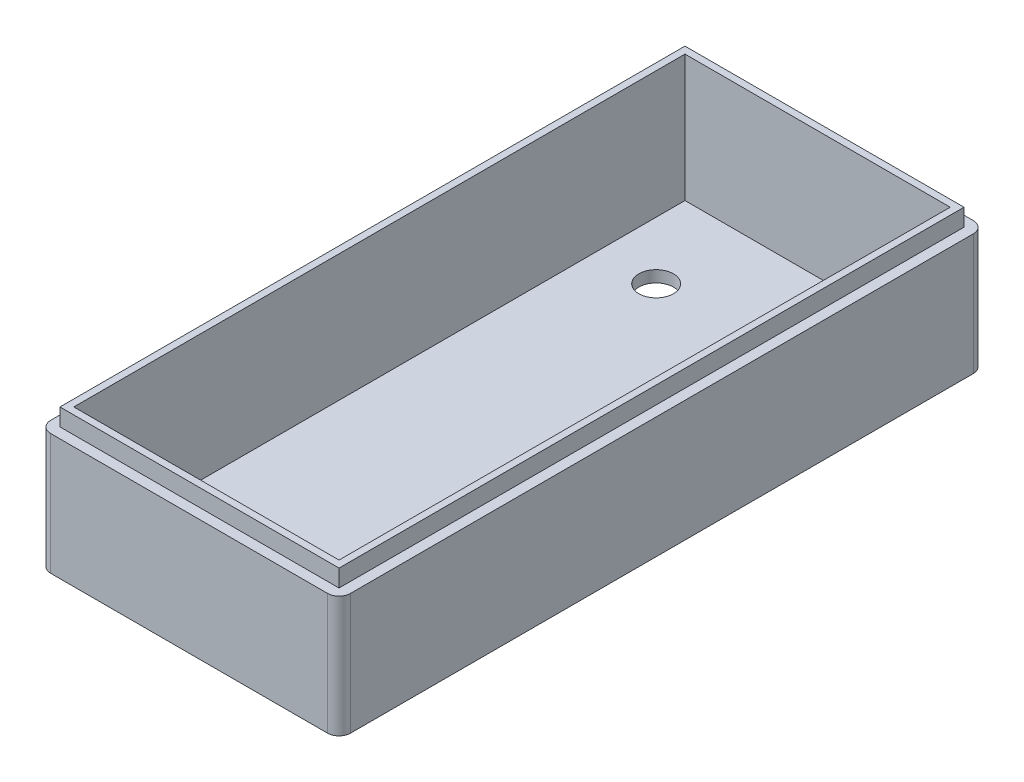
SolidWorks part; units mm, degrees
ref_plane "Front Plane" through (0, 0, 0) normal (0, 0, 1) x (1, 0, 0)
ref_plane "Top Plane" through (0, 0, 0) normal (0, 1, 0) x (1, 0, 0)
ref_plane "Right Plane" through (0, 0, 0) normal (1, 0, 0) x (0, 0, -1)
sketch "Sketch1" plane through (0, 0, 0) normal (0, 1, 0) x (1, 0, 0)
  line L1 (-77.0226, 53.0801) -> (-27.0226, 53.0801)
  line L2 (-77.0226, 53.0801) -> (-77.0226, -56.9199)
  line L3 (-77.0226, -56.9199) -> (-27.0226, -56.9199)
  line L4 (-27.0226, 53.0801) -> (-27.0226, -56.9199)
  dimension "D1" = 110
  dimension "D2" = 50
extrude "Boss-Extrude1" add sketch "Sketch1" along normal blind 2
sketch "Sketch2" plane through (0, 2, 0) normal (0, 1, 0) x (1, 0, 0)
  line L0 (-75.0226, 51.0801) -> (-75.0226, -54.9199)
  line L1 (-77.0226, 53.0801) -> (-27.0226, 53.0801)
  line L2 (-77.0226, 53.0801) -> (-77.0226, -56.9199)
  line L3 (-77.0226, -56.9199) -> (-27.0226, -56.9199)
  line L4 (-27.0226, 53.0801) -> (-27.0226, -56.9199)
  line L5 (-75.0226, -54.9199) -> (-29.0226, -54.9199)
  line L6 (-29.0226, 51.0801) -> (-29.0226, -54.9199)
  line L7 (-75.0226, 51.0801) -> (-29.0226, 51.0801)
  dimension "D1" = 2
extrude "Boss-Extrude3" add sketch "Sketch2" along normal blind 11
sketch "Sketch3" plane through (0, 2, 0) normal (0, 1, 0) x (1, 0, 0)
  circle A0 centre (-31.0226, 42.3801) radius 1.2
  circle A1 centre (-31.0226, -52.9199) radius 1.2
  circle A2 centre (-56.3226, 42.3801) radius 1.2
  circle A3 centre (-56.3226, -52.9199) radius 1.2
extrude "Boss-Extrude4" add sketch "Sketch3" along normal blind 11
sketch "Sketch4" plane through (0, 13, 0) normal (0, 1, 0) x (1, 0, 0)
  line L8 (-26.0226, 54.0801) -> (-78.0226, 54.0801)
  line L9 (-78.0226, 54.0801) -> (-78.0226, -57.9199)
  line L10 (-78.0226, -57.9199) -> (-26.0226, -57.9199)
  line L11 (-26.0226, -57.9199) -> (-26.0226, 54.0801)
  line L12 (-26.0226, 54.0801) -> (-78.0226, 54.0801)
  line L13 (-78.0226, 54.0801) -> (-78.0226, -57.9199)
  line L14 (-78.0226, -57.9199) -> (-26.0226, -57.9199)
  line L15 (-26.0226, -57.9199) -> (-26.0226, 54.0801)
  dimension "D1" = 3
extrude "Extrude-Thin1" add sketch "Sketch4" against normal blind 13 thin thin type one direction reverse wall 1
fillet "Fillet2" radius 2 4 edges at (-78.0226, 6.5, -54.0801) (-26.0226, 6.5, -54.0801) (-26.0226, 6.5, 57.9199) (-78.0226, 6.5, 57.9199)
sketch "Sketch5" plane through (0, 13, 0) normal (0, 1, 0) x (1, 0, 0)
  line L8 (-28.0226, 52.8801) -> (-76.0226, 52.8801)
  line L9 (-76.8226, 52.0801) -> (-76.8226, -55.9199)
  line L10 (-76.0226, -56.7199) -> (-28.0226, -56.7199)
  line L11 (-27.2226, -55.9199) -> (-27.2226, 52.0801)
  line L12 (-28.0226, 52.8801) -> (-76.0226, 52.8801)
  line L13 (-76.8226, 52.0801) -> (-76.8226, -55.9199)
  line L14 (-76.0226, -56.7199) -> (-28.0226, -56.7199)
  line L15 (-27.2226, -55.9199) -> (-27.2226, 52.0801)
  arc A8 (-76.0226, 52.8801) -> (-76.8226, 52.0801) centre (-76.0226, 52.0801) ccw
  arc A9 (-76.8226, -55.9199) -> (-76.0226, -56.7199) centre (-76.0226, -55.9199) ccw
  arc A10 (-28.0226, -56.7199) -> (-27.2226, -55.9199) centre (-28.0226, -55.9199) ccw
  arc A11 (-27.2226, 52.0801) -> (-28.0226, 52.8801) centre (-28.0226, 52.0801) ccw
  arc A12 (-76.0226, 52.8801) -> (-76.8226, 52.0801) centre (-76.0226, 52.0801) ccw
  arc A13 (-76.8226, -55.9199) -> (-76.0226, -56.7199) centre (-76.0226, -55.9199) ccw
  arc A14 (-28.0226, -56.7199) -> (-27.2226, -55.9199) centre (-28.0226, -55.9199) ccw
  arc A15 (-27.2226, 52.0801) -> (-28.0226, 52.8801) centre (-28.0226, 52.0801) ccw
  dimension "D1" = 1.2
extrude "Extrude-Thin3" add sketch "Sketch5" along normal blind 3 thin
sketch "Sketch6" plane through (0, 2, 0) normal (0, 1, 0) x (1, 0, 0)
  circle A0 centre (-56.3226, -52.9199) radius 1.8
  circle A1 centre (-31.0226, -52.9199) radius 1.8
  circle A2 centre (-56.3226, 42.3801) radius 1.8
  circle A3 centre (-31.0226, 42.3801) radius 1.8
extrude "Boss-Extrude5" add sketch "Sketch6" along normal blind 2.8
sketch "Sketch7" plane through (0, 2, 0) normal (0, 1, 0) x (1, 0, 0)
  line L0 (-31.0226, -52.9199) -> (-31.0226, -48.6199)
  line L1 (-31.0226, -48.6199) -> (-18.3371, -48.6199)
sketch "Sketch8" plane through (-26.0226, 0, 0) normal (1, 0, 0) x (0, 0, -1)
  line L0 (-52.9199, 2) -> (-48.6199, 2) construction
  line L2 (-48.6199, 2) -> (-40.6199, 2)
  line L3 (-48.6199, 2) -> (-48.6199, 5.6)
  line L4 (-48.6199, 5.6) -> (-40.6199, 5.6)
  line L5 (-40.6199, 2) -> (-40.6199, 5.6)
  dimension "D1" = 8
  dimension "D2" = 3.6
extrude "Cut-Extrude2" cut sketch "Sketch8" against normal blind 12.8
sketch "Sketch11" plane through (-78.0226, 0, 0) normal (-1, 0, 0) x (0, 0, 1)
  line L0 (-51.0801, 2) -> (54.9199, 2) construction
  line L1 (-50.0801, 7.8) -> (-36.9801, 7.8)
  line L2 (-50.0801, 7.8) -> (-50.0801, 2)
  line L3 (-50.0801, 2) -> (-36.9801, 2)
  line L4 (-36.9801, 7.8) -> (-36.9801, 2)
  line L5 (-51.0801, 13) -> (-51.0801, 2) construction
  dimension "D1" = 5.8
  dimension "D2" = 13.1
  dimension "D3" = 0
  dimension "D4" = 1
extrude "Cut-Extrude5" cut sketch "Sketch11" against normal blind 3
sketch "Sketch12" plane through (0, 0, 57.9199) normal (0, 0, 1) x (1, 0, 0)
  line L0 (-78.0226, 0) -> (-78.0226, 16) construction
  line L1 (-88.0226, 10.3909) -> (-18.0226, 10.3909)
  line L2 (-88.0226, 10.3909) -> (-88.0226, 20.3641)
  line L3 (-88.0226, 20.3641) -> (-18.0226, 20.3641)
  line L4 (-18.0226, 10.3909) -> (-18.0226, 20.3641)
  dimension "D1" = 70
  dimension "D2" = 10
extrude "Cut-Extrude6" cut sketch "Sketch12" against normal blind 130
sketch "Sketch13" plane through (0, 2, 0) normal (0, 1, 0) x (1, 0, 0)
  line L1 (-75.0226, 51.0801) -> (-29.0226, 51.0801)
  line L2 (-75.0226, 51.0801) -> (-75.0226, -54.9199)
  line L3 (-75.0226, -54.9199) -> (-29.0226, -54.9199)
  line L4 (-29.0226, 51.0801) -> (-29.0226, -54.9199)
extrude "Cut-Extrude7" cut sketch "Sketch13" along normal blind 130
sketch "Sketch15" plane through (0, 10.3909, 0) normal (0, 1, 0) x (1, 0, 0)
  line L8 (-76.0226, -57.9199) -> (-28.0226, -57.9199)
  line L9 (-26.0226, -55.9199) -> (-26.0226, 52.0801)
  line L10 (-28.0226, 54.0801) -> (-76.0226, 54.0801)
  line L11 (-78.0226, 52.0801) -> (-78.0226, -55.9199)
  line L12 (-76.0226, -57.9199) -> (-28.0226, -57.9199)
  line L13 (-26.0226, -55.9199) -> (-26.0226, 52.0801)
  line L14 (-28.0226, 54.0801) -> (-76.0226, 54.0801)
  line L15 (-78.0226, 52.0801) -> (-78.0226, -55.9199)
  line L20 (-75.0226, -54.9199) -> (-29.0226, -54.9199)
  line L21 (-29.0226, -54.9199) -> (-29.0226, 51.0801)
  line L22 (-29.0226, 51.0801) -> (-75.0226, 51.0801)
  line L23 (-75.0226, 51.0801) -> (-75.0226, -54.9199)
  line L24 (-75.0226, -54.9199) -> (-29.0226, -54.9199)
  line L25 (-29.0226, -54.9199) -> (-29.0226, 51.0801)
  line L26 (-29.0226, 51.0801) -> (-75.0226, 51.0801)
  line L27 (-75.0226, 51.0801) -> (-75.0226, -54.9199)
  arc A8 (-78.0226, -55.9199) -> (-76.0226, -57.9199) centre (-76.0226, -55.9199) ccw
  arc A9 (-28.0226, -57.9199) -> (-26.0226, -55.9199) centre (-28.0226, -55.9199) ccw
  arc A10 (-26.0226, 52.0801) -> (-28.0226, 54.0801) centre (-28.0226, 52.0801) ccw
  arc A11 (-76.0226, 54.0801) -> (-78.0226, 52.0801) centre (-76.0226, 52.0801) ccw
  arc A12 (-78.0226, -55.9199) -> (-76.0226, -57.9199) centre (-76.0226, -55.9199) ccw
  arc A13 (-28.0226, -57.9199) -> (-26.0226, -55.9199) centre (-28.0226, -55.9199) ccw
  arc A14 (-26.0226, 52.0801) -> (-28.0226, 54.0801) centre (-28.0226, 52.0801) ccw
  arc A15 (-76.0226, 54.0801) -> (-78.0226, 52.0801) centre (-76.0226, 52.0801) ccw
  dimension "D1" = 0
  dimension "D2" = 0
extrude "Boss-Extrude6" add sketch "Sketch15" along normal blind 60
sketch "Sketch16" plane through (0, 0, 57.9199) normal (0, 0, 1) x (1, 0, 0)
  line L0 (-76.0226, 0) -> (-28.0226, 0) construction
  line L1 (-84.3923, 79.1661) -> (-12.6524, 79.1661)
  line L2 (-84.3923, 79.1661) -> (-84.3923, 24)
  line L3 (-84.3923, 24) -> (-12.6524, 24)
  line L4 (-12.6524, 79.1661) -> (-12.6524, 24)
  dimension "D1" = 24
extrude "Cut-Extrude8" cut sketch "Sketch16" against normal blind 130
sketch "Sketch17" plane through (0, 24, 0) normal (0, 1, 0) x (1, 0, 0)
  line L16 (-76.2226, -56.1199) -> (-27.8226, -56.1199)
  line L17 (-27.8226, -56.1199) -> (-27.8226, 52.2801)
  line L18 (-27.8226, 52.2801) -> (-76.2226, 52.2801)
  line L19 (-76.2226, 52.2801) -> (-76.2226, -56.1199)
  line L20 (-76.2226, -56.1199) -> (-27.8226, -56.1199)
  line L21 (-27.8226, -56.1199) -> (-27.8226, 52.2801)
  line L22 (-27.8226, 52.2801) -> (-76.2226, 52.2801)
  line L23 (-76.2226, 52.2801) -> (-76.2226, -56.1199)
  dimension "D1" = 1.2
extrude "Cut-Extrude-Thin1" cut sketch "Sketch17" against normal blind 3 thin
sketch "Sketch18" plane through (0, 7.8, 0) normal (0, -1, 0) x (1, 0, 0)
  line L1 (-75.0226, -36.9801) -> (-78.0226, -36.9801)
  line L2 (-75.0226, -36.9801) -> (-75.0226, -50.0801)
  line L3 (-75.0226, -50.0801) -> (-78.0226, -50.0801)
  line L4 (-78.0226, -36.9801) -> (-78.0226, -50.0801)
extrude "Boss-Extrude7" add sketch "Sketch18" along normal blind 7
sketch "Sketch19" plane through (0, 5.6, 0) normal (0, -1, 0) x (1, 0, 0)
  line L1 (-29.0226, 48.6199) -> (-26.0226, 48.6199)
  line L2 (-29.0226, 48.6199) -> (-29.0226, 40.6199)
  line L3 (-29.0226, 40.6199) -> (-26.0226, 40.6199)
  line L4 (-26.0226, 48.6199) -> (-26.0226, 40.6199)
extrude "Boss-Extrude8" add sketch "Sketch19" along normal blind 4.5
sketch "Sketch20" plane through (0, 2, 0) normal (0, 1, 0) x (1, 0, 0)
  line L4 (-29.0226, 51.0801) -> (-75.0226, 51.0801) construction
  line L5 (-75.0226, -54.9199) -> (-29.0226, -54.9199) construction
  circle A0 centre (-65.0226, -39.9199) radius 6
  circle A1 centre (-65.0226, 36.0801) radius 3
  dimension "D4" = 15
  dimension "D5" = 15
extrude "Cut-Extrude9" cut sketch "Sketch20" against normal blind 4.5
